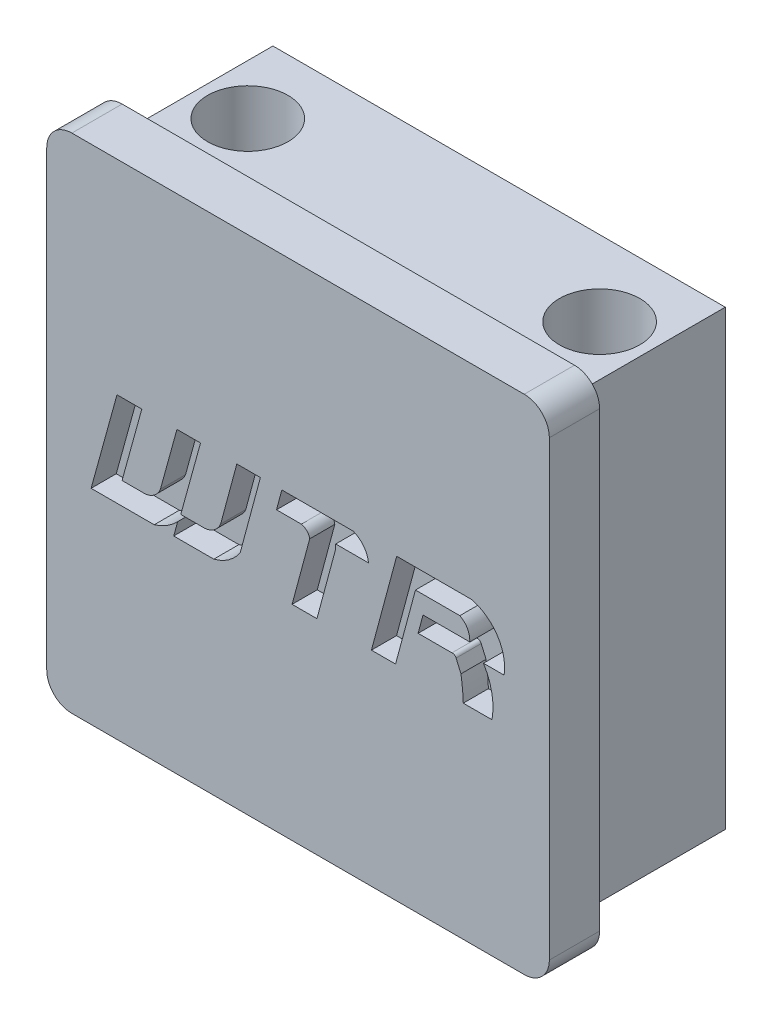
SolidWorks part; units mm, degrees
ref_plane "前视基准面" through (0, 0, 0) normal (0, 0, 1) x (1, 0, 0)
ref_plane "上视基准面" through (0, 0, 0) normal (0, 1, 0) x (1, 0, 0)
ref_plane "右视基准面" through (0, 0, 0) normal (1, 0, 0) x (0, 0, -1)
sketch "草图1" plane through (0, 0, 0) normal (0, 0, 1) x (1, 0, 0)
  line L1 (-9, -9) -> (9, -9)
  line L2 (-9, -9) -> (-9, 9)
  line L3 (-9, 9) -> (9, 9)
  line L4 (9, -9) -> (9, 9)
  line L5 (-9, -9) -> (9, 9) construction
  line L6 (-9, 9) -> (9, -9) construction
  point P0 (0, 0)
  dimension "D1" = 18
  dimension "D2" = 18
extrude "凸台-拉伸1" add sketch "草图1" along normal blind 6
sketch "草图2" plane through (0, 9, 0) normal (0, 1, 0) x (1, 0, 0)
  line L0 (-9, -6) -> (-9, 0) construction
  line L1 (0, -7.0147) -> (0, 1.2687) construction
  circle A0 centre (-7, -3) radius 1.6
  circle A1 centre (7, -3) radius 1.6
  dimension "D1" = 3.2
  dimension "D2" = 2
extrude "切除-拉伸1" cut sketch "草图2" against normal through all
sketch "草图3" plane through (0, 0, 6) normal (0, 0, 1) x (1, 0, 0)
  line L1 (-10, -10) -> (10, -10)
  line L2 (-10, -10) -> (-10, 10)
  line L3 (-10, 10) -> (10, 10)
  line L4 (10, -10) -> (10, 10)
  line L5 (-10, -10) -> (10, 10) construction
  line L6 (-10, 10) -> (10, -10) construction
  point P0 (0, 0)
  dimension "D1" = 20
  dimension "D2" = 20
extrude "凸台-拉伸2" add sketch "草图3" along normal blind 2
fillet "圆角1" radius 1 4 edges at (10, -10, 7) (-10, -10, 7) (-10, 10, 7) (10, 10, 7)
sketch "草图5" plane through (0, 0, 8) normal (0, 0, 1) x (1, 0, 0)
  line L0 (-7.2046, 1.8794) -> (-8.2345, -1.8595)
  line L1 (-8.2345, -1.8595) -> (-5.7231, -1.8595)
  line L2 (-4.9471, -1.8595) -> (-3.3528, -1.8595)
  line L3 (-7.2046, 1.8794) -> (-6.2169, 1.8794)
  line L4 (-6.2169, 1.8794) -> (-7.0035, -0.976)
  line L5 (-7.0035, -0.976) -> (-6.054, -0.976)
  line L6 (-4.8187, 1.8794) -> (-5.4778, -0.5132)
  line L7 (-4.8187, 1.8794) -> (-3.8802, 1.8794)
  line L8 (-3.8802, 1.8794) -> (-4.6668, -0.976)
  line L9 (-4.6668, -0.976) -> (-3.6964, -0.976)
  line L10 (-2.4363, 1.8794) -> (-3.0795, -0.5132)
  line L11 (-2.4363, 1.8794) -> (-1.4978, 1.8794)
  line L12 (-1.4978, 1.8794) -> (-2.3036, -1.1181)
  line L13 (-0.8571, 1.0889) -> (-0.6446, 1.8794)
  line L14 (-0.6446, 1.8794) -> (2.1962, 1.8794)
  line L15 (-0.8571, 1.0889) -> (0.1305, 1.0889)
  line L16 (1.4986, 1.0889) -> (2.8033, 1.0889)
  line L17 (-0.237, -1.8595) -> (0.464, 0.748)
  line L18 (-0.237, -1.8595) -> (0.7513, -1.8595)
  line L19 (0.7513, -1.8595) -> (1.4986, 0.9201)
  line L20 (1.4986, 1.0889) -> (1.4986, 0.9201)
  line L21 (3.925, 1.8794) -> (2.9199, -1.8595)
  line L22 (2.9199, -1.8595) -> (3.8798, -1.8595)
  line L23 (3.8798, -1.8595) -> (4.6724, 1.0889)
  line L24 (4.6724, 1.0889) -> (6.4392, 1.0889)
  line L25 (3.925, 1.8794) -> (6.9178, 1.8794)
  line L26 (7.3784, -0.0813) -> (8.1998, -0.0813)
  line L27 (6.8314, 0.3793) -> (4.9733, 0.3793)
  line L28 (4.9733, 0.3793) -> (4.7771, -0.3507)
  line L29 (4.7771, -0.3507) -> (6.1233, -0.3507)
  line L30 (6.2887, -0.4483) -> (6.482, -0.8948)
  line L31 (6.575, -1.8595) -> (7.7174, -1.8595)
  line L32 (-4.9471, -1.8595) -> (-4.7886, -1.2842)
  arc A0 (-6.054, -0.976) -> (-5.4778, -0.5132) centre (-6.1733, -0.2375) ccw
  arc A1 (-3.6964, -0.976) -> (-3.0795, -0.5132) centre (-3.7848, -0.2156) ccw
  arc A2 (0.1305, 1.0889) -> (0.464, 0.748) centre (0.0517, 0.6782) cw
  arc A3 (2.1962, 1.8794) -> (2.8033, 1.0889) centre (1.8639, 0.9959) cw
  arc A4 (6.482, -0.8948) -> (6.575, -1.8595) centre (-1.2835, -2.1302) cw
  arc A5 (7.7174, -1.8595) -> (7.3784, -0.0813) centre (5.2297, -1.4123) ccw
  arc A6 (6.2887, -0.4483) -> (6.1233, -0.3507) centre (6.139, -0.5132) ccw
  arc A7 (6.9178, 1.8794) -> (8.1998, -0.0813) centre (6.4689, 0.1864) cw
  arc A8 (-3.3528, -1.8595) -> (-2.3036, -1.1181) centre (-3.8012, -0.1118) ccw
  arc A9 (-5.7231, -1.8595) -> (-4.7886, -1.2842) centre (-6.3458, 0.1984) ccw
  arc A10 (6.8314, 0.3793) -> (6.4392, 1.0889) centre (6.0983, 0.4372) ccw
extrude "切除-拉伸2" cut sketch "草图5" against normal blind 1
